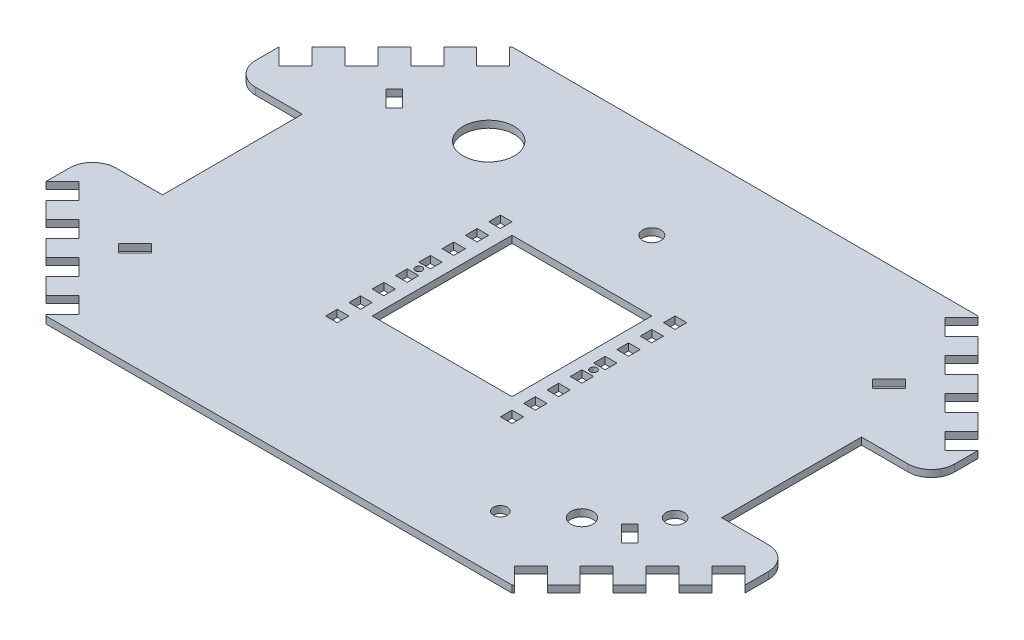
SolidWorks part; units mm, degrees
material "Balsa"
ref_plane "Plan de face" through (0, 0, 0) normal (0, 0, 1) x (1, 0, 0)
ref_plane "Plan de dessus" through (0, 0, 0) normal (0, 1, 0) x (1, 0, 0)
ref_plane "Plan de droite" through (0, 0, 0) normal (1, 0, 0) x (0, 0, -1)
sketch "Esquisse1" plane through (0, 0, 0) normal (0, 1, 0) x (1, 0, 0)
  line L1 (-150, 100) -> (150, 100)
  line L2 (-150, 100) -> (-150, -100)
  line L3 (-150, -100) -> (150, -100)
  line L4 (150, 100) -> (150, -100)
  dimension "D1" = 300
  dimension "D2" = 200
  dimension "D3" = 150
  dimension "D4" = 100
extrude "Boss.-Extru.1" add sketch "Esquisse1" along normal blind 3
sketch "Esquisse2" plane through (0, 3, 0) normal (0, 1, 0) x (1, 0, 0)
  line L0 (-100, 100) -> (-150, 50)
  line L1 (150, 100) -> (-150, 100) construction
  line L2 (-150, 100) -> (-150, -100) construction
  line L3 (-150, 50) -> (-150, 100)
  line L4 (-150, 100) -> (-100, 100)
  line L5 (150, 100) -> (150, 50)
  line L6 (150, -100) -> (150, 100) construction
  line L7 (150, 50) -> (100, 100)
  line L8 (100, 100) -> (150, 100)
  line L9 (150, -100) -> (150, -50)
  line L10 (150, -50) -> (100, -100)
  line L11 (-150, -100) -> (150, -100) construction
  line L12 (100, -100) -> (150, -100)
  line L13 (-100, -100) -> (-150, -100)
  line L14 (-150, -100) -> (-150, -50)
  line L15 (-150, -50) -> (-100, -100)
  dimension "D1" = 50
  dimension "D2" = 50
  dimension "D3" = 50
  dimension "D4" = 50
  dimension "D5" = 50
  dimension "D6" = 50
  dimension "D7" = 50
  dimension "D8" = 50
extrude "Enlèv. mat.-Extru.1" cut sketch "Esquisse2" against normal blind 10
sketch "Esquisse3" plane through (0, 3, 0) normal (0, 1, 0) x (1, 0, 0)
  line L1 (40, -40) -> (35, -40)
  line L2 (40, -40) -> (40, -35)
  line L3 (40, -35) -> (35, -35)
  line L4 (35, -40) -> (35, -35)
  dimension "D1" = 5
  dimension "D2" = 5
  dimension "D3" = 40
  dimension "D4" = 40
extrude "Enlèv. mat.-Extru.2" cut sketch "Esquisse3" against normal blind 10
pattern_linear "Répétition linéaire1" count 2 spacing 75 along (-1, 0, 0) count 8 spacing 10 along (0, 0, -1) of "Enlèv. mat.-Extru.2"
sketch "Esquisse6" plane through (0, 3, 0) normal (0, 1, 0) x (1, 0, 0)
  line L0 (-142.9289, 57.0711) -> (-150, 50)
  line L1 (-142.9289, 57.0711) -> (-135.8579, 50)
  line L2 (-150, 50) -> (-142.9289, 42.9289)
  line L3 (-135.8579, 50) -> (-142.9289, 42.9289)
  line L4 (-150, 50) -> (-100, 100) construction
  dimension "D1" = 10
  dimension "D2" = 10
  dimension "D3" = 0
extrude "Enlèv. mat.-Extru.5" cut sketch "Esquisse6" against normal blind 10
pattern_linear "Répétition linéaire2" count 4 spacing 20 along (0.7071, 0, -0.7071) of "Enlèv. mat.-Extru.5"
mirror "Symétrie1" about plane through (0, 0, 0) normal (0, 0, 1) of "Répétition linéaire2", "Enlèv. mat.-Extru.5"
sketch "Esquisse9" plane through (0, 3, 0) normal (0, 1, 0) x (1, 0, 0)
  line L3 (40, 20) -> (40, 25) construction
  line L4 (40, -5) -> (35, -5) construction
  circle A1 centre (37.5, -2.5) radius 1.5
  dimension "D1" = 2.5
  dimension "D5" = 3
  dimension "D6" = 2.5
extrude "Enlèv. mat.-Extru.8" cut sketch "Esquisse9" against normal blind 10
mirror "Symétrie2" about plane through (0, 0, 0) normal (1, 0, 0) of "Enlèv. mat.-Extru.8", "Symétrie1", "Enlèv. mat.-Extru.5", "Répétition linéaire2"
sketch "Esquisse11" plane through (0, 3, 0) normal (0, 1, 0) x (1, 0, 0)
  line L0 (150, -50) -> (150, 50) construction
  line L1 (-150, 50) -> (-150, -50) construction
  line L3 (100, 100) -> (-100, 100) construction
  line L5 (100, 100) -> (-100, 100) construction
  circle A0 centre (-70, 60) radius 11
  circle A1 centre (110, -40) radius 3.9
  circle A2 centre (90, -60) radius 4.75
  circle A3 centre (70.0715, -75.0948) radius 3
  circle A4 centre (0, 60) radius 3.95
  point P19 (0, 100)
  dimension "D1" = 22
  dimension "D2" = 80
  dimension "D3" = 6
  dimension "D4" = 40
  dimension "D5" = 9.5
  dimension "D6" = 40
  dimension "D8" = 60
  dimension "D10" = 7.8
  dimension "D11" = 140
  dimension "D12" = 7.9
  dimension "D7" = 60
  dimension "D9" = 25
  dimension "D13" = 40
extrude "Enlèv. mat.-Extru.10" cut sketch "Esquisse11" against normal blind 10
sketch "Esquisse12" plane through (0, 3, 0) normal (0, 1, 0) x (1, 0, 0)
  line L1 (30, -30) -> (-30, -30)
  line L2 (30, -30) -> (30, 30)
  line L3 (30, 30) -> (-30, 30)
  line L4 (-30, -30) -> (-30, 30)
  dimension "D1" = 30
  dimension "D2" = 60
  dimension "D3" = 30
  dimension "D4" = 60
extrude "Enlèv. mat.-Extru.11" cut sketch "Esquisse12" against normal blind 10
sketch "Esquisse13" plane through (0, 3, 0) normal (0, 1, 0) x (1, 0, 0)
  line L0 (-150, 50) -> (-150, -50) construction
  line L1 (-150, 29.9989) -> (-120, 29.9989)
  line L2 (-150, 29.9989) -> (-150, -30.0011)
  line L3 (-150, -30.0011) -> (-120, -30.0011)
  line L4 (-120, 29.9989) -> (-120, -30.0011)
  line L5 (0, 20.7878) -> (0, -24.1825) construction
  line L6 (120, 29.9989) -> (120, -30.0011)
  line L7 (150, -30.0011) -> (120, -30.0011)
  line L8 (150, 29.9989) -> (150, -30.0011)
  line L9 (150, 29.9989) -> (120, 29.9989)
  dimension "D1" = 60
  dimension "D2" = 30
  dimension "D3" = 12.93
  dimension "D4" = 12.9279
extrude "Enlèv. mat.-Extru.12" cut sketch "Esquisse13" against normal blind 10
sketch "Esquisse15" plane through (0, 3, 0) normal (0, 1, 0) x (1, 0, 0)
  line L0 (-111.4627, -57.4246) -> (-104.3916, -50.3536)
  line L1 (-104.3916, -50.3536) -> (-100.8561, -53.8891)
  line L2 (-111.4627, -57.4246) -> (-107.9271, -60.9602)
  line L3 (-107.9271, -60.9602) -> (-100.8561, -53.8891)
  line L5 (-114.6447, -71.2132) -> (-107.5736, -78.2843) construction
  line L6 (-150, -50) -> (-142.9289, -42.9289) construction
  line L8 (0, 12.4676) -> (0, -8.0255) construction
  line L9 (-11.5468, 0) -> (9.96, 0) construction
  line L10 (107.9271, -60.9602) -> (100.8561, -53.8891)
  line L11 (111.4627, -57.4246) -> (107.9271, -60.9602)
  line L12 (104.3916, -50.3536) -> (100.8561, -53.8891)
  line L13 (111.4627, -57.4246) -> (104.3916, -50.3536)
  line L14 (111.4627, 57.4246) -> (104.3916, 50.3536)
  line L15 (104.3916, 50.3536) -> (100.8561, 53.8891)
  line L16 (111.4627, 57.4246) -> (107.9271, 60.9602)
  line L17 (107.9271, 60.9602) -> (100.8561, 53.8891)
  line L18 (-107.9271, 60.9602) -> (-100.8561, 53.8891)
  line L19 (-111.4627, 57.4246) -> (-107.9271, 60.9602)
  line L20 (-104.3916, 50.3536) -> (-100.8561, 53.8891)
  line L21 (-111.4627, 57.4246) -> (-104.3916, 50.3536)
  dimension "D1" = 10
  dimension "D2" = 5
  dimension "D3" = 12
  dimension "D4" = 32.5
extrude "Enlèv. mat.-Extru.14" cut sketch "Esquisse15" against normal blind 10
fillet "Congé1" radius 10 4 edges at (-150, 1.5, 30.0011) (-150, 1.5, -29.9989) (150, 1.5, 30.0011) (150, 1.5, -29.9989)
